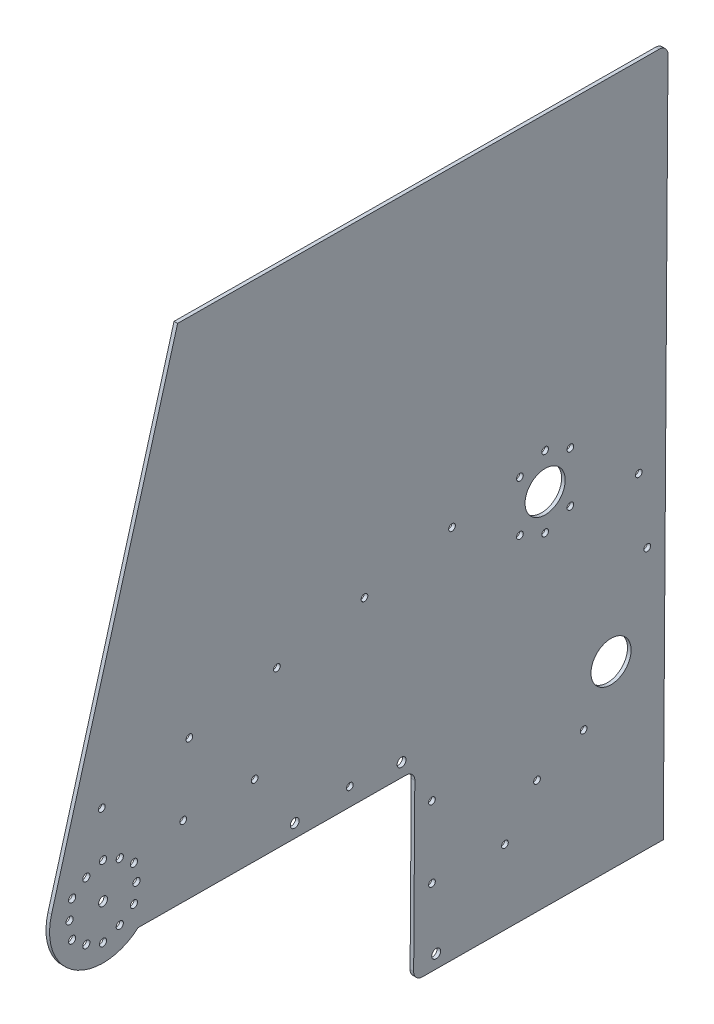
SolidWorks part; units mm, degrees
material "PC High Viscosity"
ref_plane "Front Plane" through (0, 0, 0) normal (0, 0, 1) x (1, 0, 0)
ref_plane "Top Plane" through (0, 0, 0) normal (0, 1, 0) x (1, 0, 0)
ref_plane "Right Plane" through (0, 0, 0) normal (1, 0, 0) x (0, 0, -1)
sketch "Sketch1" plane through (2097.3395, 0, 0) normal (1, 0, 0) x (0, 0, -1)
  line L0 (818.1062, 61.7756) -> (405.1402, 61.7756) construction
  line L6 (470.4626, 294.284) -> (380.6906, -25.2502)
  line L7 (442.3722, -64.3046) -> (633.0668, -65.629)
  line L8 (639.3726, -72.023) -> (638.5567, -189.4951)
  line L9 (644.8624, -195.8891) -> (816.3083, -197.0799)
  line L10 (816.3083, -197.0799) -> (819.6601, 285.5085)
  line L11 (813.3543, 291.9025) -> (470.4626, 294.284)
  line L12 (470.4626, 294.284) -> (380.6906, -25.2502)
  line L13 (442.3722, -64.3046) -> (633.0668, -65.629)
  line L14 (639.3726, -72.023) -> (638.5567, -189.4951)
  line L15 (644.8624, -195.8891) -> (816.3083, -197.0799)
  line L16 (816.3083, -197.0799) -> (819.6601, 285.5085)
  line L17 (813.3543, 291.9025) -> (470.4626, 294.284)
  circle A0 centre (553.8955, -55.5539) radius 9.525 construction
  circle A1 centre (629.9581, -56.0822) radius 9.525 construction
  circle A2 centre (654.5854, -186.4314) radius 9.525 construction
  circle A3 centre (779.0999, -68.5703) radius 25.4 construction
  arc A4 (380.6906, -25.2502) -> (442.3722, -64.3046) centre (417.3705, -35.5552) ccw
  arc A5 (639.3726, -72.023) -> (633.0668, -65.629) centre (633.0227, -71.9789) ccw
  arc A6 (638.5567, -189.4951) -> (644.8624, -195.8891) centre (644.9065, -189.5392) ccw
  arc A7 (819.6601, 285.5085) -> (813.3543, 291.9025) centre (813.3102, 285.5526) ccw
  arc A8 (380.6906, -25.2502) -> (442.3722, -64.3046) centre (417.3705, -35.5552) ccw
  arc A9 (639.3726, -72.023) -> (633.0668, -65.629) centre (633.0227, -71.9789) ccw
  arc A10 (638.5567, -189.4951) -> (644.8624, -195.8891) centre (644.9065, -189.5392) ccw
  arc A11 (819.6601, 285.5085) -> (813.3543, 291.9025) centre (813.3102, 285.5526) ccw
  circle A12 centre (553.8955, -55.5539) radius 3.175
  circle A13 centre (553.8955, -55.5539) radius 9.525 construction
  circle A14 centre (629.9581, -56.0822) radius 9.525 construction
  circle A15 centre (654.5854, -186.4314) radius 9.525 construction
  circle A16 centre (779.0999, -68.5703) radius 25.4 construction
  circle A17 centre (738.492, 61.7756) radius 25.4 construction
  circle A18 centre (738.492, 61.7756) radius 3.175
  circle A19 centre (779.0999, -68.5703) radius 3.175
  circle A20 centre (654.5854, -186.4314) radius 3.175
  circle A23 centre (417.3705, -35.5552) radius 3.175
  circle A24 centre (629.9581, -56.0822) radius 3.175
  dimension "D2" = 6.35
  dimension "D5" = 6.35
  dimension "D3" = 232.5083
  dimension "D4" = 136.525
  dimension "D1" = 0
extrude "Boss-Extrude1" add sketch "Sketch1" along normal blind 2.54
sketch "Sketch2" plane through (2099.8795, 0, 0) normal (1, 0, 0) x (0, 0, -1)
  circle A1 centre (759.6181, -100.9825) radius 2.3813
  circle A2 centre (759.6181, -100.9825) radius 2.3813
  circle A3 centre (541.1877, 46.532) radius 2.3813
  circle A4 centre (541.1877, 46.532) radius 2.3812
  circle A5 centre (478.8516, 34.4297) radius 2.3813
  circle A6 centre (478.8516, 34.4297) radius 2.3813
  circle A7 centre (416.5156, 22.3274) radius 2.3813
  circle A8 centre (416.5156, 22.3274) radius 2.3813
  circle A9 centre (525.3205, -14.245) radius 2.3813
  circle A10 centre (525.3205, -14.245) radius 2.3813
  circle A11 centre (798.8869, 37.4794) radius 2.3813
  circle A12 centre (798.8869, 37.4794) radius 2.3813
  circle A13 centre (665.8598, 70.7367) radius 2.3813
  circle A14 centre (665.8598, 70.7367) radius 2.3812
  circle A15 centre (603.5237, 58.6344) radius 2.3813
  circle A16 centre (603.5237, 58.6344) radius 2.3812
  circle A17 centre (703.5591, -143.5195) radius 2.3813
  circle A18 centre (703.5591, -143.5195) radius 2.3813
  circle A19 centre (726.3842, -115.3922) radius 2.3813
  circle A20 centre (726.3842, -115.3922) radius 2.3813
  circle A21 centre (804.8987, -11.2496) radius 2.3813
  circle A22 centre (804.8987, -11.2496) radius 2.3813
  circle A23 centre (474.5205, -14.245) radius 2.3813
  circle A24 centre (474.5205, -14.245) radius 2.3813
  circle A25 centre (651.59, -141.5513) radius 2.3813
  circle A26 centre (651.59, -141.5513) radius 2.3813
  circle A27 centre (651.59, -90.7513) radius 2.3813
  circle A28 centre (651.59, -90.7513) radius 2.3813
  circle A29 centre (593.1285, -52.6513) radius 2.3813
  circle A30 centre (593.1285, -52.6513) radius 2.3813
  dimension "D1" = 0
  dimension "D2" = 0
  dimension "D3" = 0
  dimension "D4" = 0
  dimension "D5" = 0
  dimension "D6" = 0
  dimension "D7" = 0
  dimension "D8" = 0
  dimension "D9" = 0
  dimension "D10" = 0
  dimension "D11" = 0
  dimension "D12" = 0
  dimension "D13" = 0
  dimension "D14" = 0
  dimension "D15" = 0
extrude "Cut-Extrude1" cut sketch "Sketch2" against normal through all
sketch "Sketch4" plane through (2099.8795, 0, 0) normal (1, 0, 0) x (0, 0, -1)
  line L0 (-4.7879, -2.7643) -> (0, -5.5286)
  line L1 (0, -5.5286) -> (4.7879, -2.7643)
  line L2 (4.7879, -2.7643) -> (4.7879, 2.7643)
  line L3 (4.7879, 2.7643) -> (0, 5.5286)
  line L4 (0, 5.5286) -> (-4.7879, 2.7643)
  line L5 (-4.7879, 2.7643) -> (-4.7879, -2.7643)
  circle A0 centre (-11.9062, 20.6222) radius 2.5527
  circle A1 centre (0, 25.4) radius 2.5527
  circle A2 centre (-23.8125, 0) radius 2.5527
  circle A3 centre (-21.997, 12.7) radius 2.5527
  circle A4 centre (-11.9062, -20.6222) radius 2.5527
  circle A5 centre (-21.997, -12.7) radius 2.5527
  circle A6 centre (11.9062, -20.6222) radius 2.5527
  circle A7 centre (0, -25.4) radius 2.5527
  circle A8 centre (23.8125, 0) radius 2.5527
  circle A9 centre (21.997, -12.7) radius 2.5527
  circle A10 centre (11.9062, 20.6222) radius 2.5527
  circle A11 centre (21.997, 12.7) radius 2.5527
  circle A12 centre (0, 0) radius 30.1625
sketch "Sketch5" plane through (2099.8795, 0, 0) normal (1, 0, 0) x (0, 0, -1)
  line L0 (395.3735, -22.8552) -> (405.4643, -14.933) construction
  line L1 (405.4643, -14.933) -> (417.3705, -10.1552) construction
  line L2 (417.3705, -10.1552) -> (429.2768, -14.933) construction
  line L3 (429.2768, -14.933) -> (439.3675, -22.8552) construction
  line L4 (439.3675, -22.8552) -> (441.183, -35.5552) construction
  line L5 (441.183, -35.5552) -> (439.3675, -48.2552) construction
  line L6 (439.3675, -48.2552) -> (429.2768, -56.1775) construction
  line L7 (429.2768, -56.1775) -> (417.3705, -60.9552) construction
  line L8 (417.3705, -60.9552) -> (405.4643, -56.1775) construction
  line L9 (405.4643, -56.1775) -> (395.3735, -48.2552) construction
  line L10 (395.3735, -48.2552) -> (393.558, -35.5552) construction
  line L11 (393.558, -35.5552) -> (395.3735, -22.8552) construction
  circle A1 centre (417.3705, -35.5552) radius 3.175 construction
  circle A2 centre (395.3735, -48.2552) radius 2.5527
  circle A3 centre (417.3705, -35.5552) radius 3.175 construction
  circle A4 centre (405.4643, -56.1775) radius 2.5527
  circle A6 centre (395.3735, -22.8552) radius 2.5527
  circle A8 centre (393.558, -35.5552) radius 2.5527
  circle A10 centre (417.3705, -10.1552) radius 2.5527
  circle A12 centre (405.4643, -14.933) radius 2.5527
  circle A14 centre (439.3675, -22.8552) radius 2.5527
  circle A16 centre (429.2768, -14.933) radius 2.5527
  circle A18 centre (439.3675, -48.2552) radius 2.5527
  circle A20 centre (441.183, -35.5552) radius 2.5527
  circle A22 centre (417.3705, -60.9552) radius 2.5527
  circle A24 centre (429.2768, -56.1775) radius 2.5527
extrude "Cut-Extrude2" cut sketch "Sketch5" against normal through all
extrude "Cut-Extrude3" cut sketch "Sketch6" along normal through all
sketch "Sketch6" plane through (2099.8795, 0, 0) normal (-1, 0, 0) x (0, 0, 1)
  circle A1 centre (-714.2134, 41.676) radius 2.3812
  circle A5 centre (-714.2134, 77.5972) radius 2.3812
  circle A6 centre (-732.1738, 85.0366) radius 2.3812
  circle A7 centre (-750.1343, 77.5972) radius 2.3812
  circle A10 centre (-750.1343, 41.676) radius 2.3812
  circle A11 centre (-732.1738, 34.2366) radius 2.3812
  circle A13 centre (-732.1738, 59.6366) radius 14.1605
sketch "Sketch7" plane through (2099.8795, 0, 0) normal (1, 0, 0) x (0, 0, -1)
  circle A0 centre (732.1738, 59.6366) radius 14.1605 construction
  circle A1 centre (732.1738, 59.6366) radius 14.1605
  circle A2 centre (732.1738, 59.6366) radius 2.3812
  circle A3 centre (750.1343, 41.676) radius 2.3813 construction
extrude "Boss-Extrude2" add sketch "Sketch7" against normal up to surface (2.54 mm away) up to face at (2097.3395, 77.5972, -711.8322)
sketch "Sketch8" plane through (2097.3395, 0, 0) normal (-1, 0, 0) x (0, 0, 1)
  circle A0 centre (-732.1738, 59.6366) radius 14.2875
  circle A1 centre (-779.0999, -68.5703) radius 14.2875
  dimension "D1" = 28.575
extrude "Cut-Extrude4" cut sketch "Sketch8" against normal through all
